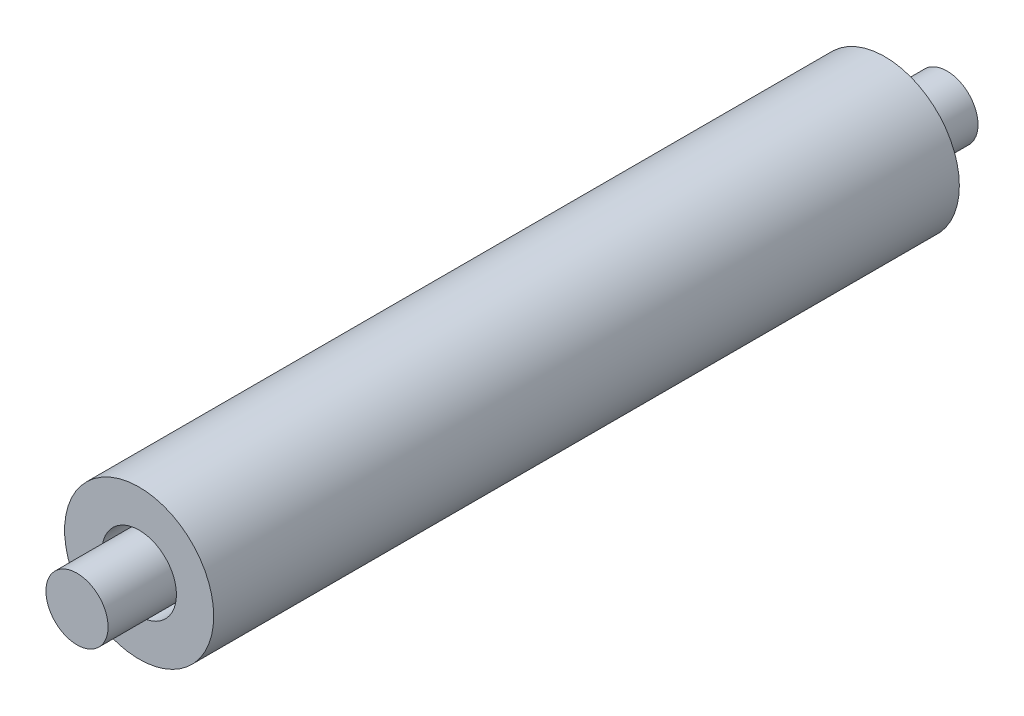
SolidWorks part; units mm, degrees
ref_plane "Front Plane" through (0, 0, 0) normal (0, 0, 1) x (1, 0, 0)
ref_plane "Top Plane" through (0, 0, 0) normal (0, 1, 0) x (1, 0, 0)
ref_plane "Right Plane" through (0, 0, 0) normal (1, 0, 0) x (0, 0, -1)
sketch "Sketch1" plane through (0, 0, 0) normal (0, 0, 1) x (1, 0, 0)
  circle A0 centre (0, 0) radius 1.25
  dimension "D1" = 2.5
extrude "CentralAxis" add sketch "Sketch1" along normal mid plane 35
sketch "Sketch2" plane through (0, 0, 0) normal (0, 0, 1) x (1, 0, 0)
  circle A0 centre (0, 0) radius 3
  circle A1 centre (0, 0) radius 1.5
  dimension "D1" = 3
  dimension "D2" = 6
extrude "RollingAxis" add sketch "Sketch2" along normal mid plane 30
